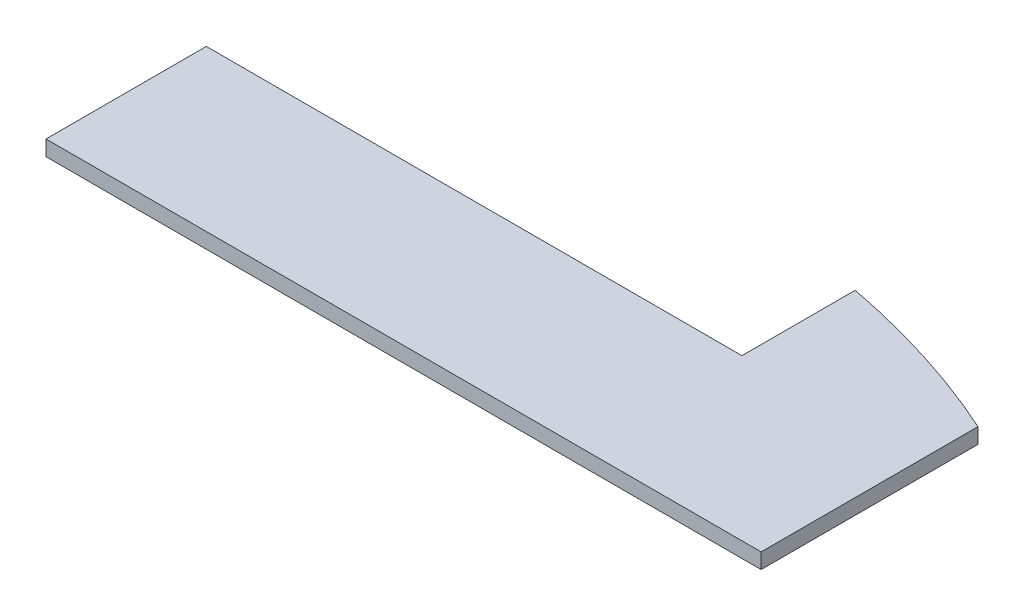
SolidWorks part; units mm, degrees
ref_plane "Front Plane" through (0, 0, 0) normal (0, 0, 1) x (1, 0, 0)
ref_plane "Top Plane" through (0, 0, 0) normal (0, 1, 0) x (1, 0, 0)
ref_plane "Right Plane" through (0, 0, 0) normal (1, 0, 0) x (0, 0, -1)
sketch "Sketch1" plane through (0, 0, 0) normal (0, 1, 0) x (1, 0, 0)
  line L0 (0, 0) -> (74.5, 0)
  line L1 (74.5, 0) -> (74.5, 22.5921)
  line L3 (55.8, 28.4901) -> (55.8, 16.7)
  line L4 (55.8, 16.7) -> (0, 16.7)
  line L5 (0, 16.7) -> (0, 0)
  line L6 (0, 16.7) -> (55.8, 16.7) construction
  line L10 (0, 0) -> (74.5, 0) construction
  line L11 (55.8, 28.4901) -> (55.8, 16.7) construction
  ellipse E0 centre (39.7282, -35) end of major axis (-35.2718, -35) minor radius 65 construction
  ellipse E1 centre (39.7282, -35) end of major axis (-35.2718, -35) minor radius 65 (74.5, 22.5921) -> (55.8, 28.4901) ccw
extrude "Boss-Extrude1" add sketch "Sketch1" along normal blind 1.6
